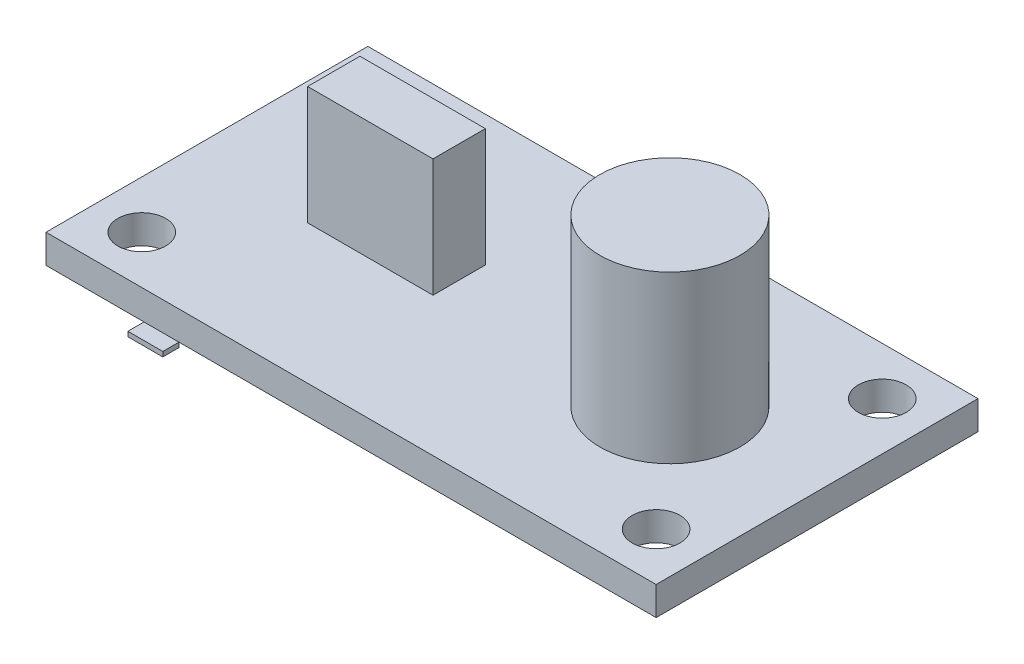
SolidWorks part; units mm, degrees
ref_plane "Front Plane" through (0, 0, 0) normal (0, 0, 1) x (1, 0, 0)
ref_plane "Top Plane" through (0, 0, 0) normal (0, 1, 0) x (1, 0, 0)
ref_plane "Right Plane" through (0, 0, 0) normal (1, 0, 0) x (0, 0, -1)
sketch "Sketch1" plane through (0, 0, 0) normal (0, 1, 0) x (1, 0, 0)
  line L1 (-19.2397, 15.8322) -> (18.9903, 15.8322)
  line L2 (-19.2397, 15.8322) -> (-19.2397, -4.3378)
  line L3 (-19.2397, -4.3378) -> (18.9903, -4.3378)
  line L4 (18.9903, 15.8322) -> (18.9903, -4.3378)
  line L5 (-14.4194, -4.3378) -> (-10.9288, -4.3378)
  line L6 (-14.4194, -4.3378) -> (-14.4194, -5.3478)
  line L7 (-14.4194, -5.3478) -> (-10.9288, -5.3478)
  line L8 (-10.9288, -4.3378) -> (-10.9288, -5.3478)
  line L9 (-10.9288, 8.075) -> (-3.0702, 8.075)
  line L10 (-10.9288, 8.075) -> (-10.9288, 3.5362)
  line L11 (-10.9288, 3.5362) -> (-3.0702, 3.5362)
  line L12 (-3.0702, 8.075) -> (-3.0702, 3.5362)
  circle A0 centre (-16.2397, 12.8322) radius 1.5
  circle A1 centre (15.9903, 12.8322) radius 1.5
  circle A2 centre (15.9903, -1.3378) radius 1.5
  circle A3 centre (-16.2397, -1.3378) radius 1.5
  circle A4 centre (7.5723, 5.7472) radius 4.5797
  point P8 (-12.6741, -5.3478)
  point P23 (18.9903, 5.7472)
  dimension "D6" = 3
  dimension "D7" = 3
  dimension "D8" = 3
  dimension "D9" = 3
  dimension "D1" = 38.23
  dimension "D2" = 20.17
  dimension "D3" = 21.18
  dimension "D4" = 3
  dimension "D5" = 3
  dimension "D10" = 3
  dimension "D11" = 3
  dimension "D12" = 3
  dimension "D13" = 3
  dimension "D14" = 3
  dimension "D15" = 3
  dimension "D16" = 0
extrude "Boss-Extrude1" add sketch "Sketch1" against normal blind 1.8 contours L2 L3 L4 L1 | A3 | A0 | A2 | A1
sketch "Sketch5" plane through (0, -1.8, 0) normal (0, -1, 0) x (1, 0, 0)
  line L0 (-19.2397, 4.3378) -> (18.9903, 4.3378) construction
  line L1 (-13.0988, 4.3378) -> (-10.9096, 4.3378)
  line L2 (-13.0988, 4.3378) -> (-13.0988, 5.3478)
  line L3 (-13.0988, 5.3478) -> (-10.9096, 5.3478)
  line L4 (-10.9096, 4.3378) -> (-10.9096, 5.3478)
  line L5 (-19.2397, -15.8322) -> (18.9903, -15.8322) construction
  dimension "D1" = 21.18
extrude "Boss-Extrude2" add sketch "Sketch5" along normal blind 0.3 separate body
sketch "Sketch6" plane through (0, -1.8, 0) normal (0, -1, 0) x (-1, 0, 0)
  line L0 (-18.9903, 15.8322) -> (-18.9903, -4.3378) construction
  circle A0 centre (-9.7704, 5.7472) radius 4.3901
  point P4 (-18.9903, 5.7472)
  dimension "D1" = 0
extrude "Boss-Extrude3" add sketch "Sketch6" against normal blind 12.2
sketch "Sketch7" plane through (0, -1.8, 0) normal (0, -1, 0) x (-1, 0, 0)
  line L1 (11.552, 4.3682) -> (3.6964, 4.3682)
  line L2 (11.552, 4.3682) -> (11.552, 7.6485)
  line L3 (11.552, 7.6485) -> (3.6964, 7.6485)
  line L4 (3.6964, 4.3682) -> (3.6964, 7.6485)
extrude "Boss-Extrude4" add sketch "Sketch7" against normal blind 9.2
